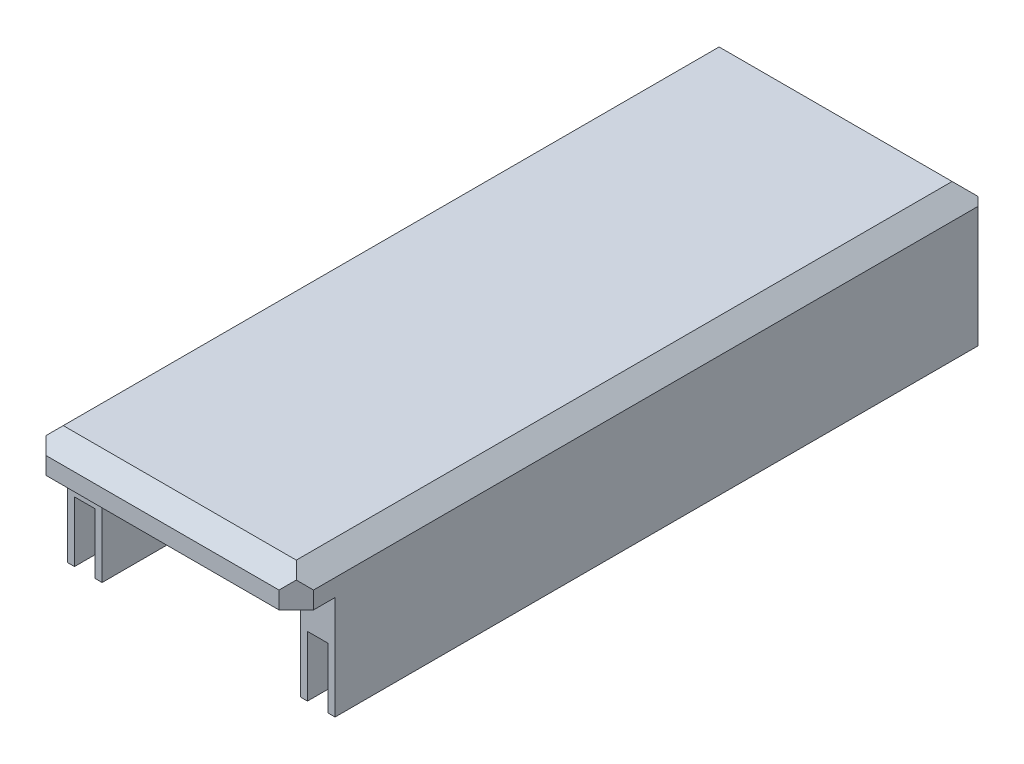
SolidWorks part; units mm, degrees
ref_plane "Front Plane" through (0, 0, 0) normal (0, 0, 1) x (1, 0, 0)
ref_plane "Top Plane" through (0, 0, 0) normal (0, 1, 0) x (1, 0, 0)
ref_plane "Right Plane" through (0, 0, 0) normal (1, 0, 0) x (0, 0, -1)
sketch "Sketch1" plane through (0, 0, 0) normal (0, 1, 0) x (1, 0, 0)
  line L1 (-16.3548, 68.5175) -> (14.6452, 68.5175)
  line L2 (-16.3548, 68.5175) -> (-16.3548, -11.4825)
  line L3 (-16.3548, -11.4825) -> (14.6452, -11.4825)
  line L4 (14.6452, 68.5175) -> (14.6452, -11.4825)
  dimension "D1" = 31
  dimension "D2" = 80
extrude "Boss-Extrude1" add sketch "Sketch1" along normal blind 4 contours L2 L1 L4 L3
sketch "Sketch2" plane through (0, 0, 0) normal (0, -1, 0) x (1, 0, 0)
  line L0 (-16.3548, 11.4825) -> (14.6452, 11.4825) construction
  line L1 (-12.8548, 9.4825) -> (11.1452, 9.4825)
  line L2 (-12.8548, 9.4825) -> (-12.8548, 6.9825)
  line L3 (-12.8548, 6.9825) -> (11.1452, 6.9825)
  line L4 (11.1452, 9.4825) -> (11.1452, 6.9825)
  line L5 (-16.3548, -68.5175) -> (-16.3548, 11.4825) construction
  dimension "D1" = 24
  dimension "D2" = 2.5
  dimension "D3" = 2
  dimension "D4" = 3.5
extrude "Cut-Extrude1" cut sketch "Sketch2" against normal blind 3 contours L2 L1 L4 L3
sketch "Sketch3" plane through (0, 0, 0) normal (0, -1, 0) x (1, 0, 0)
  line L0 (-16.3548, -68.5175) -> (-16.3548, 11.4825) construction
  line L1 (-16.3548, 6.9825) -> (-12.3548, 6.9825)
  line L2 (-16.3548, 6.9825) -> (-16.3548, -68.5175)
  line L3 (-16.3548, -68.5175) -> (-12.3548, -68.5175)
  line L4 (-12.3548, 6.9825) -> (-12.3548, -64.5175)
  line L5 (-16.3548, -68.5175) -> (14.6452, -68.5175) construction
  line L6 (14.6452, -68.5175) -> (14.6452, 11.4825) construction
  line L7 (14.6452, 6.9825) -> (10.6452, 6.9825)
  line L8 (14.6452, 6.9825) -> (14.6452, -68.5175)
  line L9 (14.6452, -68.5175) -> (10.6452, -68.5175)
  line L10 (10.6452, 6.9825) -> (10.6452, -64.5175)
  line L12 (-12.3548, -68.5175) -> (10.6452, -68.5175)
  line L14 (-12.3548, -64.5175) -> (10.6452, -64.5175)
  line L16 (-12.8548, 6.9825) -> (11.1452, 6.9825) construction
  dimension "D1" = 4
  dimension "D2" = 4
  dimension "D3" = 4
  dimension "D4" = 0
  dimension "D5" = 0
extrude "Boss-Extrude2" add sketch "Sketch3" along normal blind 12 contours L7 L10 L14 L4 L1 L2 L3 L12 L9 L8
sketch "Sketch4" plane through (0, -12, 0) normal (0, -1, 0) x (1, 0, 0)
  line L0 (-12.3548, 6.9825) -> (-12.3548, -64.5175) construction
  line L1 (-15.5548, 6.9825) -> (-13.1548, 6.9825)
  line L2 (-15.5548, 6.9825) -> (-15.5548, -67.7175)
  line L3 (-15.5548, -67.7175) -> (-13.1548, -67.7175)
  line L4 (-13.1548, 6.9825) -> (-13.1548, -65.3175)
  line L6 (14.6452, -68.5175) -> (-16.3548, -68.5175) construction
  line L7 (14.6452, 6.9825) -> (10.6452, 6.9825) construction
  line L8 (-13.1548, -67.7175) -> (-12.1548, -67.7175)
  line L10 (-13.1548, -65.3175) -> (-12.1548, -65.3175)
  line L11 (-12.1548, -67.7175) -> (-12.1548, -65.3175)
  line L12 (11.4452, 6.9825) -> (13.8452, 6.9825)
  line L13 (11.4452, 6.9825) -> (11.4452, -65.3175)
  line L14 (11.4452, -67.7175) -> (13.8452, -67.7175)
  line L15 (13.8452, 6.9825) -> (13.8452, -67.7175)
  line L16 (10.6452, 6.9825) -> (10.6452, -64.5175) construction
  line L18 (11.4452, -67.7175) -> (10.4452, -67.7175)
  line L20 (11.4452, -65.3175) -> (10.4452, -65.3175)
  line L21 (10.4452, -67.7175) -> (10.4452, -65.3175)
  dimension "D1" = 2.4
  dimension "D2" = 0.8
  dimension "D3" = 0.8
  dimension "D4" = 2.4
  dimension "D5" = 1
  dimension "D6" = 2.4
  dimension "D7" = 0.8
  dimension "D8" = 0.8
  dimension "D9" = 1
extrude "Cut-Extrude3" cut sketch "Sketch4" against normal blind 7
sketch "Sketch5" plane through (0, -12, 0) normal (0, -1, 0) x (1, 0, 0)
  line L0 (-12.1548, -67.7175) -> (-12.1548, -65.3175) construction
  line L1 (-12.1548, -64.5175) -> (10.4756, -64.5175)
  line L2 (-12.1548, -64.5175) -> (-12.1548, -68.5175)
  line L3 (-12.1548, -68.5175) -> (10.4756, -68.5175)
  line L4 (10.4756, -64.5175) -> (10.4756, -68.5175)
  line L5 (14.6452, -68.5175) -> (-16.3548, -68.5175) construction
  line L6 (-12.3548, -64.5175) -> (10.6452, -64.5175) construction
  dimension "D1" = 0
extrude "Boss-Extrude3" add sketch "Sketch5" along normal blind 2 contours L2 L1 L4 L3
chamfer "Chamfer1" distance 2 angle 45 2 edges at (-16.3548, 2, 11.4825) (14.6452, 2, 11.4825)
chamfer "Chamfer2" distance 2 angle 45 1 edges at (-0.8548, 4, 11.4825)
chamfer "Chamfer3" distance 2 angle 45 2 edges at (14.6452, 4, -29.5175) (-16.3548, 4, -29.5175)
chamfer "Chamfer4" distance 2 angle 45 1 edges at (-0.8548, 4, -68.5175)
chamfer "Chamfer6" distance 1 angle 45 2 edges at (14.6452, -5, -68.5175) (-16.3548, -5, -68.5175)
